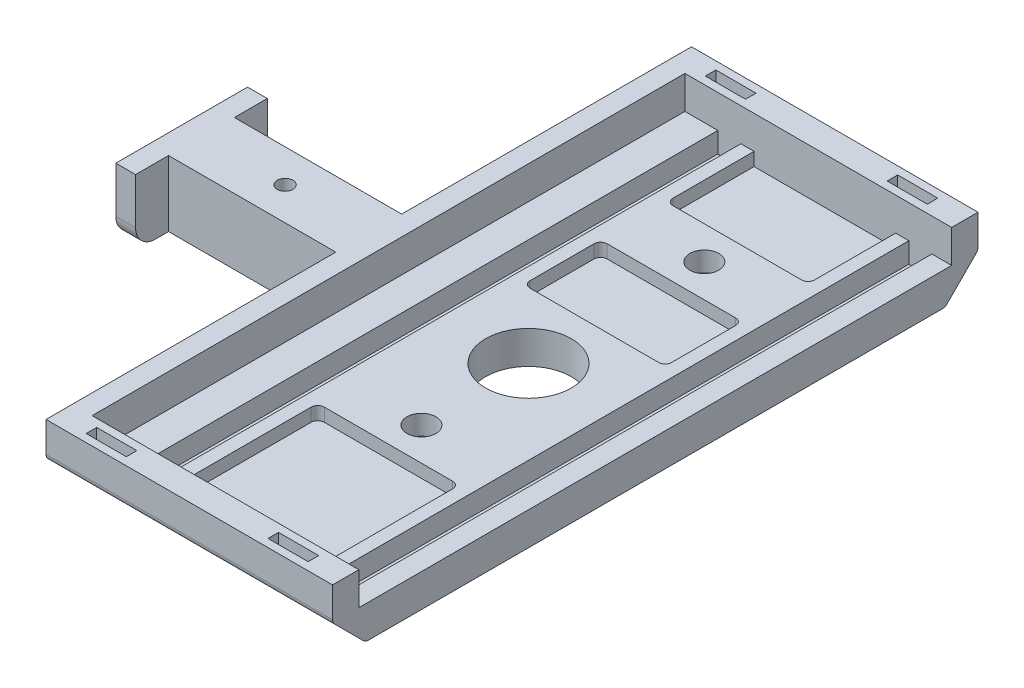
SolidWorks part; units mm, degrees
ref_plane "Front Plane" through (0, 0, 0) normal (0, 0, 1) x (1, 0, 0)
ref_plane "Top Plane" through (0, 0, 0) normal (0, 1, 0) x (1, 0, 0)
ref_plane "Right Plane" through (0, 0, 0) normal (1, 0, 0) x (0, 0, -1)
sketch "Sketch2" plane through (0, 0, 0) normal (0, 0, 1) x (1, 0, 0)
  line L0 (-19.25, 0) -> (19.25, 0)
  line L1 (19.25, 0) -> (19.25, 5)
  line L2 (19.25, 5) -> (16.25, 5)
  line L3 (16.25, 5) -> (16.25, 1.9)
  line L4 (16.25, 1.9) -> (12.75, 1.9)
  line L5 (12.75, 1.9) -> (12.75, 5)
  line L6 (12.75, 5) -> (-12.75, 5)
  line L7 (-12.75, 5) -> (-12.75, 1.9)
  line L8 (-12.75, 1.9) -> (-16.25, 1.9)
  line L9 (-16.25, 1.9) -> (-16.25, 5)
  line L10 (-16.25, 5) -> (-19.25, 5)
  line L11 (-19.25, 5) -> (-19.25, 0)
  line L12 (-14.5, 1.9) -> (14.5, 1.9) construction
  point P12 (0, 0)
  dimension "D1" = 3.5
  dimension "D2" = 3.5
  dimension "D3" = 3.1
  dimension "D4" = 3
  dimension "D5" = 3
  dimension "D6" = 5
  dimension "D7" = 25.5
extrude "Boss-Extrude1" add sketch "Sketch2" along normal mid plane 90
sketch "Sketch3" plane through (0, 0, 0) normal (0, -1, 0) x (1, 0, 0)
  circle A0 centre (0, 0) radius 6.5
  dimension "D1" = 13
extrude "Cut-Extrude1" cut sketch "Sketch3" against normal through all
sketch "Sketch5" plane through (0, 0, 0) normal (0, 0, 1) x (1, 0, 0)
  line L0 (-19.25, 0) -> (-24.25, 0)
  line L1 (-24.25, 0) -> (-24.25, 10)
  line L2 (-24.25, 10) -> (-19.25, 10)
  line L3 (-19.25, 10) -> (-19.25, 0)
  line L4 (-16.25, 5) -> (-19.25, 5) construction
  dimension "D1" = 5
  dimension "D2" = 5
extrude "Boss-Extrude2" add sketch "Sketch5" along normal through all and the other way through all
sketch "Sketch8" plane through (0, 0, 45) normal (0, 0, 1) x (1, 0, 0)
  line L1 (-24.25, 10) -> (19.25, 10)
  line L2 (-24.25, 10) -> (-24.25, 0)
  line L3 (-24.25, 0) -> (19.25, 0)
  line L4 (19.25, 10) -> (19.25, 0)
extrude "Boss-Extrude3" add sketch "Sketch8" along normal blind 3
mirror "Mirror1" about plane through (0, 0, 0) normal (0, 0, 1) of "Boss-Extrude3"
other "Move Face1" face at (-2.5, 5, -48) parameters "D1"=1
other "Move Face2" face at (-2.5, 5, 48) parameters "D1"=1
sketch "Sketch10" plane through (0, 10, 0) normal (0, 1, 0) x (1, 0, 0)
  line L0 (-13.35, -47.7) -> (-19.25, -47.7) construction
  line L1 (-19.25, -47.7) -> (-19.25, -46.3) construction
  line L2 (-19.25, -46.3) -> (-13.35, -46.3) construction
  line L3 (-13.35, -46.3) -> (-13.35, -47.7) construction
  line L4 (14.25, -47.7) -> (8.35, -47.7) construction
  line L5 (8.35, -47.7) -> (8.35, -46.3) construction
  line L6 (8.35, -46.3) -> (14.25, -46.3) construction
  line L7 (14.25, -46.3) -> (14.25, -47.7) construction
  line L8 (14.25, 46.3) -> (8.35, 46.3) construction
  line L9 (8.35, 46.3) -> (8.35, 47.7) construction
  line L10 (8.35, 47.7) -> (14.25, 47.7) construction
  line L11 (14.25, 47.7) -> (14.25, 46.3) construction
  line L12 (-13.35, 46.3) -> (-19.25, 46.3) construction
  line L13 (-19.25, 46.3) -> (-19.25, 47.7) construction
  line L14 (-19.25, 47.7) -> (-13.35, 47.7) construction
  line L15 (-13.35, 47.7) -> (-13.35, 46.3) construction
  line L16 (-13.35, -47.7) -> (-19.25, -47.7)
  line L17 (-19.25, -47.7) -> (-19.25, -46.3)
  line L18 (-19.25, -46.3) -> (-13.35, -46.3)
  line L19 (-13.35, -46.3) -> (-13.35, -47.7)
  line L20 (14.25, -47.7) -> (8.35, -47.7)
  line L21 (8.35, -47.7) -> (8.35, -46.3)
  line L22 (8.35, -46.3) -> (14.25, -46.3)
  line L23 (14.25, -46.3) -> (14.25, -47.7)
  line L24 (14.25, 46.3) -> (8.35, 46.3)
  line L25 (8.35, 46.3) -> (8.35, 47.7)
  line L26 (8.35, 47.7) -> (14.25, 47.7)
  line L27 (14.25, 47.7) -> (14.25, 46.3)
  line L28 (-13.35, 46.3) -> (-19.25, 46.3)
  line L29 (-19.25, 46.3) -> (-19.25, 47.7)
  line L30 (-19.25, 47.7) -> (-13.35, 47.7)
  line L31 (-13.35, 47.7) -> (-13.35, 46.3)
  line L32 (-13.25, 46.2) -> (-19.35, 46.2)
  line L33 (-19.35, 46.2) -> (-19.35, 47.8)
  line L34 (-19.35, 47.8) -> (-13.25, 47.8)
  line L35 (-13.25, 47.8) -> (-13.25, 46.2)
  line L36 (14.35, 46.2) -> (8.25, 46.2)
  line L37 (8.25, 46.2) -> (8.25, 47.8)
  line L38 (8.25, 47.8) -> (14.35, 47.8)
  line L39 (14.35, 47.8) -> (14.35, 46.2)
  line L40 (-13.25, -47.8) -> (-19.35, -47.8)
  line L41 (-19.35, -47.8) -> (-19.35, -46.2)
  line L42 (-19.35, -46.2) -> (-13.25, -46.2)
  line L43 (-13.25, -46.2) -> (-13.25, -47.8)
  line L44 (14.35, -47.8) -> (8.25, -47.8)
  line L45 (8.25, -47.8) -> (8.25, -46.2)
  line L46 (8.25, -46.2) -> (14.35, -46.2)
  line L47 (14.35, -46.2) -> (14.35, -47.8)
  dimension "D1" = 0.1
extrude "Cut-Extrude2" cut sketch "Sketch10" against normal blind 3.5 contours L39 L38 L37 L36 L26 L27 L24 L25 | L27 L26 L25 L24 | L31 L30 L29 L28 | L35 L34 L33 L32 L30 L31 L28 L29 | L19 L18 L17 L16 | L43 L42 L41 L40 L18 L19 L16 L17 | L47 L46 L45 L44 L22 L23 L20 L21
hole_wizard "CBORE for M2 SHCS1" positions "Sketch14" profile "Sketch15" counterbore size "M2" standard "ANSI Metric" end condition through all
sketch "Sketch14" plane through (0, 5, 0) normal (0, 1, 0) x (1, 0, 0)
  point P0 (0, 26.7)
  point P2 (0, -16.25)
  dimension "D1" = 16.25
  dimension "D2" = 26.7
sketch "Sketch15" plane through (0, 5, -26.7) normal (1, 0, 0) x (0, 0, 1)
  line L0 (0, 0) -> (0, 5)
  line L1 (0, 5) -> (1.2, 5)
  line L3 (1.2, 5) -> (1.2, 3)
  line L4 (1.2, 3) -> (2.2, 3)
  line L5 (2.2, 3) -> (2.2, 0)
  line L7 (2.2, 0) -> (0, 0)
  line L11 (0, -6.35) -> (0, 107.95) construction
  dimension "Thru Hole Dia." = 2.4
  dimension "Thru Hole Depth" = 5
  dimension "C'Bore Dia." = 4.4
  dimension "C'Bore Depth" = 3
sketch "Sketch11" plane through (0, 0, 0) normal (0, -1, 0) x (1, 0, 0)
  line L1 (-2.55, 9.55) -> (2.55, 9.55)
  line L2 (-2.55, 9.55) -> (-2.55, 7.95)
  line L3 (-2.55, 7.95) -> (2.55, 7.95)
  line L4 (2.55, 9.55) -> (2.55, 7.95)
  line L5 (-2.55, 9.55) -> (2.55, 7.95) construction
  line L6 (-2.55, 7.95) -> (2.55, 9.55) construction
  line L7 (-2.55, -18.4) -> (2.55, -18.4)
  line L8 (-2.55, -18.4) -> (-2.55, -20)
  line L9 (-2.55, -20) -> (2.55, -20)
  line L10 (2.55, -18.4) -> (2.55, -20)
  line L11 (-2.55, -18.4) -> (2.55, -20) construction
  line L12 (-2.55, -20) -> (2.55, -18.4) construction
  point P0 (0, 8.75)
  point P5 (0, -19.2)
  dimension "D1" = 1.6
  dimension "D2" = 5.1
  dimension "D3" = 19.2
  dimension "D4" = 8.75
extrude "Cut-Extrude3" [suppressed] cut sketch "Sketch11" against normal through all
sketch "Sketch12" plane through (-24.25, 0, 0) normal (-1, 0, 0) x (0, 0, 1)
  line L0 (49, 10) -> (-49, 10) construction
  line L1 (-5, 10) -> (5, 10)
  line L2 (-5, 10) -> (-5, 0)
  line L3 (-5, 0) -> (5, 0)
  line L4 (5, 10) -> (5, 0)
  line L5 (49, 0) -> (-49, 0) construction
  point P8 (0, 0)
  dimension "D1" = 10
extrude "Boss-Extrude4" add sketch "Sketch12" along normal blind 25.4
sketch "Sketch13" plane through (0, 0, 0) normal (0, 0, 1) x (1, 0, 0)
  line L1 (-49.65, 10) -> (-52.65, 10)
  line L2 (-49.65, 10) -> (-49.65, 0)
  line L3 (-49.65, 0) -> (-52.65, 0)
  line L4 (-52.65, 10) -> (-52.65, 0)
  dimension "D1" = 3
extrude "Boss-Extrude5" add sketch "Sketch13" along normal mid plane 20
fillet "Fillet1" radius 3 2 edges at (-51.15, 0, 10) (-51.15, 0, -10)
chamfer "Chamfer1" distance 5 angle 45 2 edges at (-2.5, 0, -49) (-2.5, 0, 49)
fillet "Fillet2" radius 1 4 edges at (-2.5, 0, 44) (-2.5, 5, 49) (-2.5, 0, -44) (-2.5, 5, -49)
fillet "Fillet3" [suppressed] radius 1
other "Move Face3" face at (-19.25, 7.5, 0) parameters "D1"=2
hole_wizard "M2 Clearance Hole1" positions "Sketch16" profile "Sketch17" hole size "M2" standard "ANSI Metric" end condition through all
sketch "Sketch16" plane through (0, 10, 0) normal (0, 1, 0) x (1, 0, 0)
  line L0 (-36.95, 0) -> (-36.95, 5) construction
  line L2 (-49.65, 5) -> (-24.25, 5) construction
  point P2 (-36.95, 0)
sketch "Sketch17" plane through (-36.95, 10, 0) normal (1, 0, 0) x (0, 0, 1)
  line L0 (0, 0) -> (0, 10)
  line L1 (0, 10) -> (1.2, 10)
  line L2 (1.2, 10) -> (1.2, 0)
  line L5 (1.2, 0) -> (0, 0)
  line L11 (0, -6.35) -> (0, 107.95) construction
  dimension "Thru Hole Dia." = 2.4
  dimension "Thru Hole Depth" = 10
sketch "Sketch18" plane through (0, 5, 0) normal (0, 1, 0) x (1, 0, 0)
  line L0 (12.75, -45) -> (12.75, 45) construction
  line L1 (-10.75, -45) -> (10.75, -45)
  line L2 (-10.75, -45) -> (-10.75, -21.25)
  line L3 (-10.75, -21.25) -> (10.75, -21.25)
  line L4 (10.75, -45) -> (10.75, -21.25)
  line L5 (-10.75, 10) -> (10.75, 10)
  line L6 (-10.75, 10) -> (-10.75, 21.7)
  line L7 (-10.75, 21.7) -> (10.75, 21.7)
  line L8 (10.75, 10) -> (10.75, 21.7)
  line L9 (-10.75, 31.7) -> (10.75, 31.7)
  line L10 (-10.75, 31.7) -> (-10.75, 45)
  line L11 (-10.75, 45) -> (10.75, 45)
  line L12 (10.75, 31.7) -> (10.75, 45)
  line L15 (19.25, 45) -> (-21.25, 45) construction
  line L16 (19.25, -45) -> (-21.25, -45) construction
  circle A0 centre (0, -16.25) radius 2.2 construction
  circle A1 centre (0, 0) radius 6.5 construction
  circle A2 centre (0, 26.7) radius 2.2 construction
  point P12 (0, -21.25)
  point P26 (0, 10)
  point P27 (0, 31.7)
  point P28 (0, 21.7)
  dimension "D1" = 2
  dimension "D3" = 5
  dimension "D4" = 10
  dimension "D5" = 5
  dimension "D6" = 5
extrude "Cut-Extrude4" cut sketch "Sketch18" against normal blind 2
fillet "Fillet4" radius 1 8 edges at (10.75, 4, -31.7) (-10.75, 4, -31.7) (10.75, 4, -10) (10.75, 4, -21.7) (-10.75, 4, -21.7) (-10.75, 4, -10) (10.75, 4, 21.25) (-10.75, 4, 21.25)
equation "\"D2@Sketch2\"=\"D1@Sketch2\""
